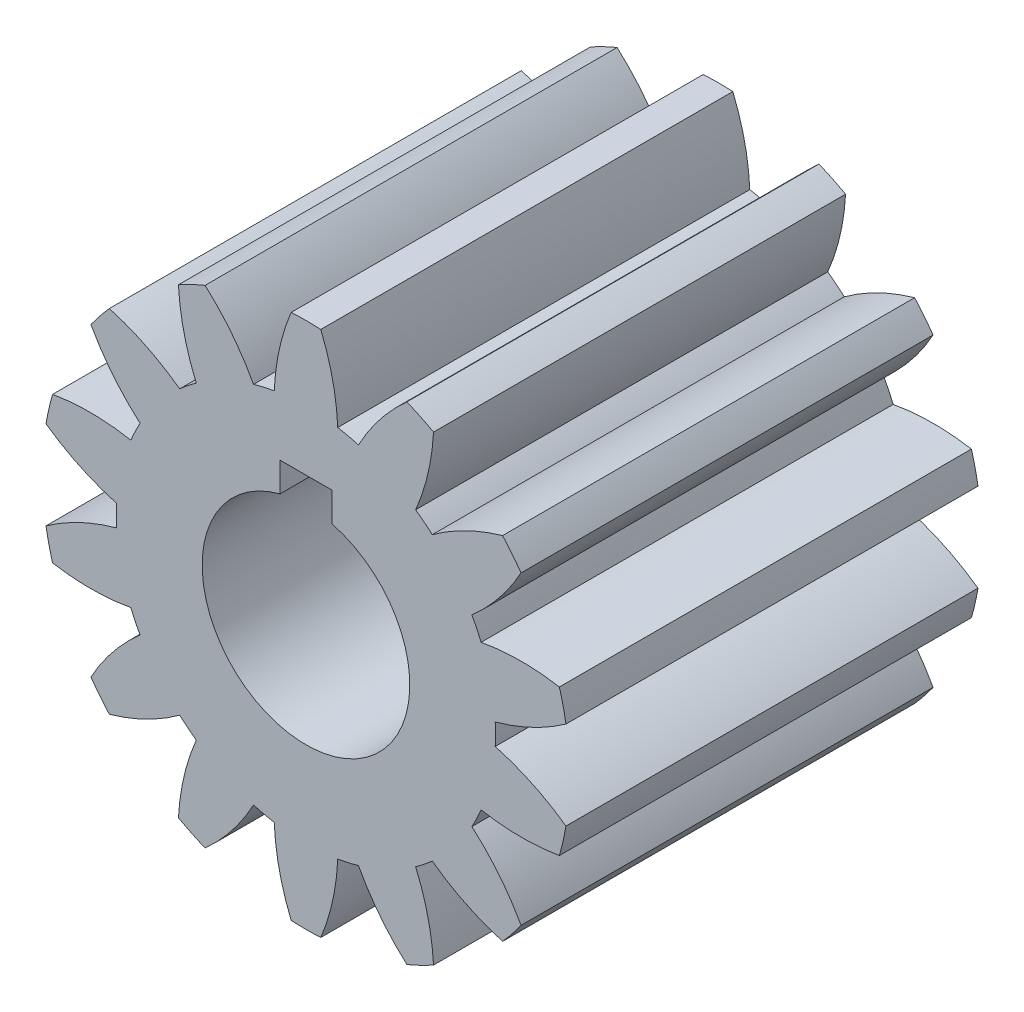
SolidWorks part; units mm, degrees
ref_plane "Front Plane" through (0, 0, 0) normal (0, 0, 1) x (1, 0, 0)
ref_plane "Top Plane" through (0, 0, 0) normal (0, 1, 0) x (1, 0, 0)
ref_plane "Right Plane" through (0, 0, 0) normal (1, 0, 0) x (0, 0, -1)
ref_plane "Plane1" through (0, 0, 15.875) normal (0, 0, 1) x (1, 0, 0)
sketch "Sketch1" plane through (0, 0, 15.875) normal (0, 0, 1) x (1, 0, 0)
  line L0 (1, 5) -> (1, 3.873)
  line L1 (-1, 3.873) -> (-1, 5)
  line L2 (-1, 5) -> (1, 5)
  arc A0 (1, 3.873) -> (-1, 3.873) centre (0, 0) cw
  arc A1 (-3.8881, 9.3866) -> (-4.9146, 8.8923) centre (0, 0) ccw
  arc A2 (-4.9146, 8.8923) -> (-4.2257, 5.9556) centre (3.6995, 9.3637) ccw
  arc A3 (-4.2257, 5.9556) -> (-4.866, 5.4451) centre (0, 0) ccw
  arc A4 (-4.866, 5.4451) -> (-7.5757, 6.7701) centre (-9.9522, -1.5231) ccw
  arc A5 (-7.5757, 6.7701) -> (-8.2861, 5.8793) centre (0, 0) ccw
  arc A6 (-8.2861, 5.8793) -> (-6.3913, 3.5324) centre (-0.7297, 10.0416) ccw
  arc A7 (-6.3913, 3.5324) -> (-6.7466, 2.7945) centre (0, 0) ccw
  arc A8 (-6.7466, 2.7945) -> (-9.7629, 2.8126) centre (-8.3058, -5.6903) ccw
  arc A9 (-9.7629, 2.8126) -> (-10.0164, 1.7019) centre (0, 0) ccw
  arc A10 (-10.0164, 1.7019) -> (-7.291, 0.4095) centre (-5.0143, 8.7306) ccw
  arc A11 (-7.291, 0.4095) -> (-7.291, -0.4095) centre (0, 0) ccw
  arc A12 (-7.291, -0.4095) -> (-10.0164, -1.7019) centre (-5.0143, -8.7306) ccw
  arc A13 (-10.0164, -1.7019) -> (-9.7629, -2.8126) centre (0, 0) ccw
  arc A14 (-9.7629, -2.8126) -> (-6.7466, -2.7945) centre (-8.3058, 5.6903) ccw
  arc A15 (-6.7466, -2.7945) -> (-6.3913, -3.5324) centre (0, 0) ccw
  arc A16 (-6.3913, -3.5324) -> (-8.2861, -5.8793) centre (-0.7297, -10.0416) ccw
  arc A17 (-8.2861, -5.8793) -> (-7.5757, -6.7701) centre (0, 0) ccw
  arc A18 (-7.5757, -6.7701) -> (-4.866, -5.4451) centre (-9.9522, 1.5231) ccw
  arc A19 (-4.866, -5.4451) -> (-4.2257, -5.9556) centre (0, 0) ccw
  arc A20 (-4.2257, -5.9556) -> (-4.9146, -8.8923) centre (3.6995, -9.3637) ccw
  arc A21 (-4.9146, -8.8923) -> (-3.8881, -9.3866) centre (0, 0) ccw
  arc A22 (-3.8881, -9.3866) -> (-2.0216, -7.0171) centre (-9.6274, -2.9458) ccw
  arc A23 (-2.0216, -7.0171) -> (-1.2232, -7.1993) centre (0, 0) ccw
  arc A24 (-1.2232, -7.1993) -> (-0.5697, -10.144) centre (7.3959, -6.8313) ccw
  arc A25 (-0.5697, -10.144) -> (0.5697, -10.144) centre (0, 0) ccw
  arc A26 (0.5697, -10.144) -> (1.2232, -7.1993) centre (-7.3959, -6.8313) ccw
  arc A27 (1.2232, -7.1993) -> (2.0216, -7.0171) centre (0, 0) ccw
  arc A28 (2.0216, -7.0171) -> (3.8881, -9.3866) centre (9.6274, -2.9458) ccw
  arc A29 (3.8881, -9.3866) -> (4.9146, -8.8923) centre (0, 0) ccw
  arc A30 (4.9146, -8.8923) -> (4.2257, -5.9556) centre (-3.6995, -9.3637) ccw
  arc A31 (4.2257, -5.9556) -> (4.866, -5.4451) centre (0, 0) ccw
  arc A32 (4.866, -5.4451) -> (7.5757, -6.7701) centre (9.9522, 1.5231) ccw
  arc A33 (7.5757, -6.7701) -> (8.2861, -5.8793) centre (0, 0) ccw
  arc A34 (8.2861, -5.8793) -> (6.3913, -3.5324) centre (0.7297, -10.0416) ccw
  arc A35 (6.3913, -3.5324) -> (6.7466, -2.7945) centre (0, 0) ccw
  arc A36 (6.7466, -2.7945) -> (9.7629, -2.8126) centre (8.3058, 5.6903) ccw
  arc A37 (9.7629, -2.8126) -> (10.0164, -1.7019) centre (0, 0) ccw
  arc A38 (10.0164, -1.7019) -> (7.291, -0.4095) centre (5.0143, -8.7306) ccw
  arc A39 (7.291, -0.4095) -> (7.291, 0.4095) centre (0, 0) ccw
  arc A40 (7.291, 0.4095) -> (10.0164, 1.7019) centre (5.0143, 8.7306) ccw
  arc A41 (10.0164, 1.7019) -> (9.7629, 2.8126) centre (0, 0) ccw
  arc A42 (9.7629, 2.8126) -> (6.7466, 2.7945) centre (8.3058, -5.6903) ccw
  arc A43 (6.7466, 2.7945) -> (6.3913, 3.5324) centre (0, 0) ccw
  arc A44 (6.3913, 3.5324) -> (8.2861, 5.8793) centre (0.7297, 10.0416) ccw
  arc A45 (8.2861, 5.8793) -> (7.5757, 6.7701) centre (0, 0) ccw
  arc A46 (7.5757, 6.7701) -> (4.866, 5.4451) centre (9.9522, -1.5231) ccw
  arc A47 (4.866, 5.4451) -> (4.2257, 5.9556) centre (0, 0) ccw
  arc A48 (4.2257, 5.9556) -> (4.9146, 8.8923) centre (-3.6995, 9.3637) ccw
  arc A49 (4.9146, 8.8923) -> (3.8881, 9.3866) centre (0, 0) ccw
  arc A50 (3.8881, 9.3866) -> (2.0216, 7.0171) centre (9.6274, 2.9458) ccw
  arc A51 (2.0216, 7.0171) -> (1.2232, 7.1993) centre (0, 0) ccw
  arc A52 (1.2232, 7.1993) -> (0.5697, 10.144) centre (-7.3959, 6.8313) ccw
  arc A53 (0.5697, 10.144) -> (-0.5697, 10.144) centre (0, 0) ccw
  arc A54 (-0.5697, 10.144) -> (-1.2232, 7.1993) centre (7.3959, 6.8313) ccw
  arc A55 (-1.2232, 7.1993) -> (-2.0216, 7.0171) centre (0, 0) ccw
  arc A56 (-2.0216, 7.0171) -> (-3.8881, 9.3866) centre (-9.6274, 2.9458) ccw
extrude "Boss-Extrude1" add sketch "Sketch1" against normal blind 15.875
